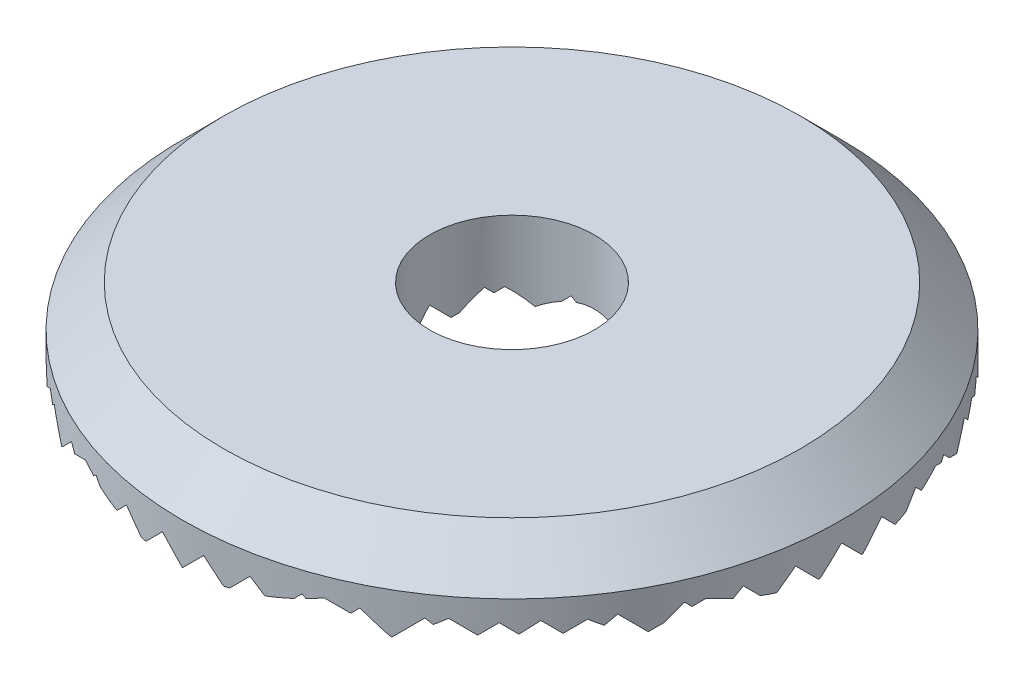
SolidWorks part; units mm, degrees
ref_plane "Front Plane" through (0, 0, 0) normal (0, 0, 1) x (1, 0, 0)
ref_plane "Top Plane" through (0, 0, 0) normal (0, 1, 0) x (1, 0, 0)
ref_plane "Right Plane" through (0, 0, 0) normal (1, 0, 0) x (0, 0, -1)
sketch "Sketch1" plane through (0, 0, 0) normal (0, 1, 0) x (1, 0, 0)
  circle A0 centre (0, 0) radius 8
  circle A1 centre (0, 0) radius 2
  dimension "D1" = 4
  dimension "D2" = 16
extrude "Boss-Extrude1" add sketch "Sketch1" along normal blind 2
chamfer "Chamfer1" distance 1 angle 45 1 edges at (0, 2, 8)
sketch "Sketch2" plane through (0, 0, 0) normal (0, 0, 1) x (1, 0, 0)
  line L0 (-8, 0.5) -> (8.2534, 0.5) construction
  line L1 (-8, 1) -> (-8, 0) construction
  line L3 (-8, 0) -> (-7.5, 0.5)
  line L4 (-7.5, 0.5) -> (-7, 0)
  line L5 (-8, 0) -> (8, 0) construction
  line L6 (-7, 0) -> (-6.5, 0.5)
  line L7 (-6.5, 0.5) -> (-6, 0)
  line L8 (-6, 0) -> (-5.5, 0.5)
  line L9 (-5.5, 0.5) -> (-5, 0)
  line L10 (-5, 0) -> (-4.5, 0.5)
  line L11 (-4.5, 0.5) -> (-4, 0)
  line L12 (-4, 0) -> (-3.5, 0.5)
  line L13 (-3.5, 0.5) -> (-3, 0)
  line L14 (-3, 0) -> (-2.5, 0.5)
  line L15 (-2.5, 0.5) -> (-2, 0)
  line L16 (-2, 0) -> (-1.5, 0.5)
  line L17 (-1.5, 0.5) -> (-1, 0)
  line L18 (-1, 0) -> (-0.5, 0.5)
  line L19 (-0.5, 0.5) -> (0, 0)
  line L20 (0, 0) -> (0.5, 0.5)
  line L21 (0.5, 0.5) -> (1, 0)
  line L22 (1, 0) -> (1.5, 0.5)
  line L23 (1.5, 0.5) -> (2, 0)
  line L24 (2, 0) -> (2.5, 0.5)
  line L25 (2.5, 0.5) -> (3, 0)
  line L26 (3, 0) -> (3.5, 0.5)
  line L27 (3.5, 0.5) -> (4, 0)
  line L28 (4, 0) -> (4.5, 0.5)
  line L29 (4.5, 0.5) -> (5, 0)
  line L30 (5, 0) -> (5.5, 0.5)
  line L31 (5.5, 0.5) -> (6, 0)
  line L32 (6, 0) -> (6.5, 0.5)
  line L33 (6.5, 0.5) -> (7, 0)
  line L34 (7, 0) -> (7.5, 0.5)
  line L35 (7.5, 0.5) -> (8, 0)
  line L36 (8, 0) -> (-8, 0)
  point P4 (8.2534, 0.5)
extrude "Cut-Extrude2" cut sketch "Sketch2" against normal through all and the other way through all contours L36 L4 L3 | L36 L7 L6 | L36 L9 L8 | L36 L11 L10 | L36 L13 L12 | L36 L15 L14 | L36 L17 L16 | L36 L19 L18 | L36 L21 L20 | L36 L23 L22 | L36 L25 L24 | L36 L27 L26 | L36 L29 L28 | L36 L31 L30 | L36 L33 L32 | L36 L35 L34
sketch "Sketch3" plane through (0, 0, 0) normal (1, 0, 0) x (0, 0, -1)
  line L0 (-8, 0) -> (-7.4569, 0.5431)
  line L1 (-7.4569, 0.5431) -> (-6.9138, 0)
  line L2 (7.4162, 0) -> (-7.4162, 0) construction
  line L3 (-6.9138, 0) -> (-6.3737, 0.5401)
  line L4 (-6.3737, 0.5401) -> (-5.8336, 0)
  line L5 (6.245, 0) -> (-6.245, 0) construction
  line L6 (-5.8336, 0) -> (-5.2966, 0.5371)
  line L7 (-5.2966, 0.5371) -> (-4.7595, 0)
  line L8 (5.2915, 0) -> (-5.2915, 0) construction
  line L9 (-4.7595, 0) -> (-4.2254, 0.5341)
  line L10 (-4.2254, 0.5341) -> (-3.6913, 0)
  line L11 (3.873, 0) -> (-3.873, 0) construction
  line L12 (-3.6913, 0) -> (-3.1602, 0.5311)
  line L13 (-3.1602, 0.5311) -> (-2.6291, 0)
  line L14 (-2.6291, 0) -> (-2.1009, 0.5282)
  line L15 (-2.1009, 0.5282) -> (-1.5728, 0)
  line L16 (-1.5728, 0) -> (-1.0475, 0.5252)
  line L17 (-1.0475, 0.5252) -> (-0.5223, 0)
  line L18 (-0.5223, 0) -> (0, 0.5223)
  line L19 (0, 0.5223) -> (0.5223, 0)
  line L20 (0.5223, 0) -> (1.0417, 0.5194)
  line L21 (1.0417, 0.5194) -> (1.5611, 0)
  line L22 (1.5611, 0) -> (2.0776, 0.5165)
  line L23 (2.0776, 0.5165) -> (2.5941, 0)
  line L24 (2.5941, 0) -> (3.1078, 0.5136)
  line L25 (3.1078, 0.5136) -> (3.6214, 0)
  line L26 (3.6214, 0) -> (4.1322, 0.5108)
  line L27 (4.1322, 0.5108) -> (4.643, 0)
  line L28 (4.643, 0) -> (5.1509, 0.5079)
  line L29 (5.1509, 0.5079) -> (5.6589, 0)
  line L30 (5.6589, 0) -> (6.164, 0.5051)
  line L31 (6.164, 0.5051) -> (6.6691, 0)
  line L32 (6.9282, 0) -> (-6.9282, 0) construction
  line L33 (6.6691, 0) -> (7.1714, 0.5023)
  line L34 (7.1714, 0.5023) -> (8, 0)
  line L35 (-7.4569, 0.5431) -> (8, 0.5) construction
  line L36 (8, 0) -> (8, 1) construction
  line L37 (0, 0) -> (0, 0.5223) construction
  line L38 (-8, 0) -> (8, 0)
  point P3 (0, 0)
extrude "Cut-Extrude4" cut sketch "Sketch3" against normal through all both and the other way through all contours L33 L38 L34 | L30 L38 L31 | L28 L38 L29 | L26 L38 L27 | L24 L38 L25 | L20 L38 L21 | L22 L38 L23 | L18 L38 L19 | L16 L38 L17 | L14 L38 L15 | L12 L38 L13 | L9 L38 L10 | L6 L38 L7 | L3 L38 L4 | L0 L38 L1
